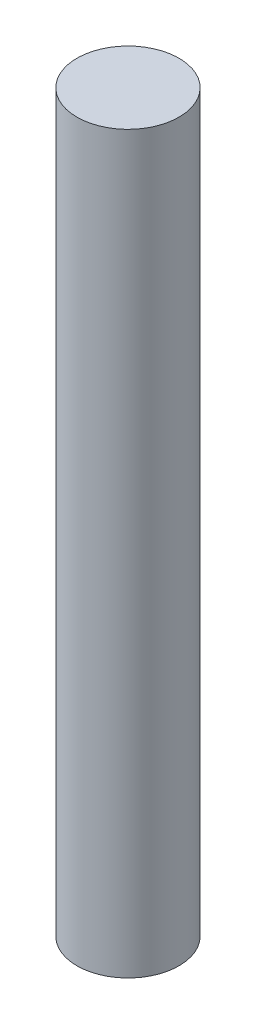
SolidWorks part; units mm, degrees
ref_plane "Front Plane" through (0, 0, 0) normal (0, 0, 1) x (1, 0, 0)
ref_plane "Top Plane" through (0, 0, 0) normal (0, 1, 0) x (1, 0, 0)
ref_plane "Right Plane" through (0, 0, 0) normal (1, 0, 0) x (0, 0, -1)
sketch "Sketch1" plane through (0, 0, 0) normal (0, 1, 0) x (1, 0, 0)
  circle A0 centre (0, 0) radius 12.5
  dimension "D1" = 25
extrude "Boss-Extrude1" add sketch "Sketch1" along normal mid plane 180
sketch "Sketch2" [suppressed] plane through (0, 0, 0) normal (0, 0, 1) x (1, 0, 0)
  line L0 (-46.307, 295) -> (67.1241, 295)
  line L1 (12.5, 300) -> (-12.5, 300) construction
  line L2 (-46.307, 295) -> (-46.307, 195)
  line L3 (-46.307, 195) -> (58.77, 195)
  dimension "D1" = 5
  dimension "D2" = 100
split line "Split Line1" [suppressed]
chamfer "Chamfer1" [suppressed] distance 2 angle 45
